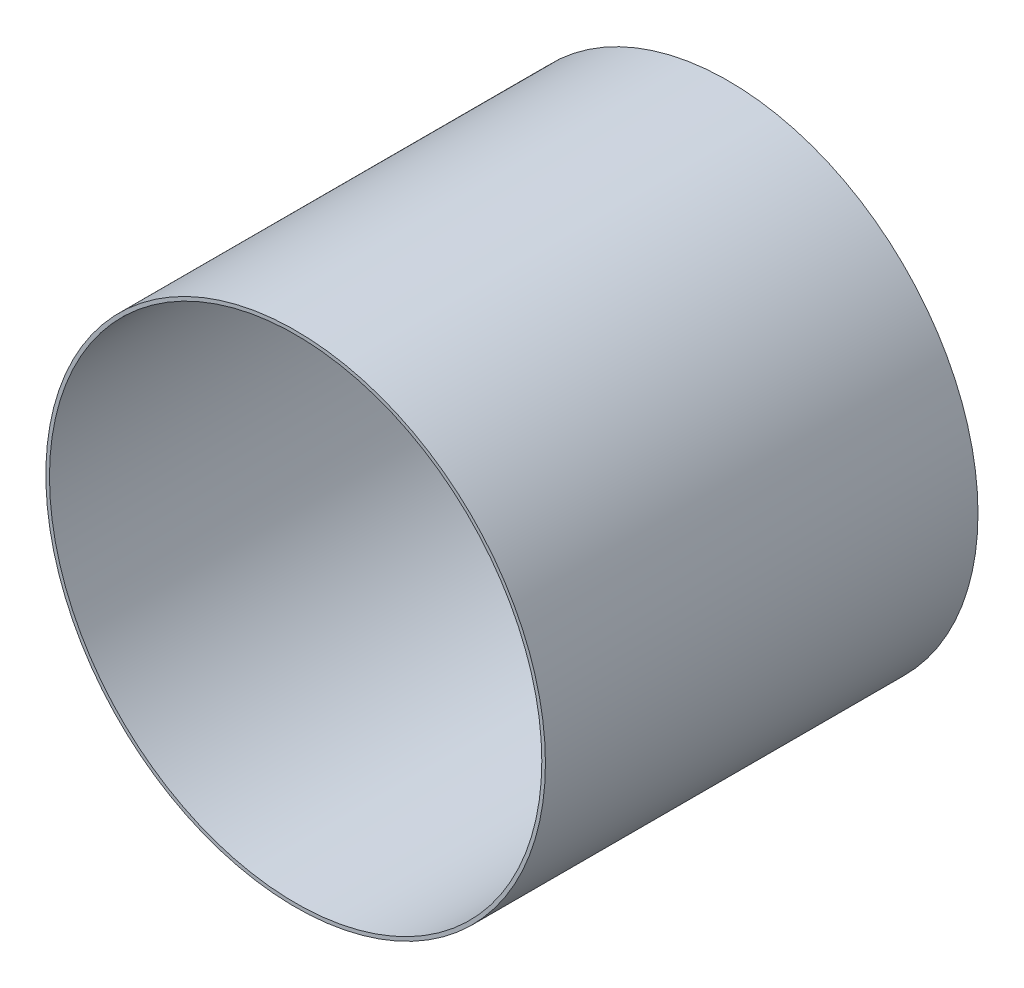
SolidWorks part; units mm, degrees
material "Titanio"
ref_plane "Piano frontale" through (0, 0, 0) normal (0, 0, 1) x (1, 0, 0)
ref_plane "Piano superiore" through (0, 0, 0) normal (0, 1, 0) x (1, 0, 0)
ref_plane "Piano destro" through (0, 0, 0) normal (1, 0, 0) x (0, 0, -1)
sketch "Schizzo1" plane through (0, 0, 0) normal (0, 0, 1) x (1, 0, 0)
  circle A0 centre (0, 0) radius 448.3
  circle A1 centre (0, 0) radius 441.8
  dimension "D1" = 896.6
  dimension "D2" = 6.5
extrude "Estrusione-Estrusione1" add sketch "Schizzo1" along normal blind 776.3
